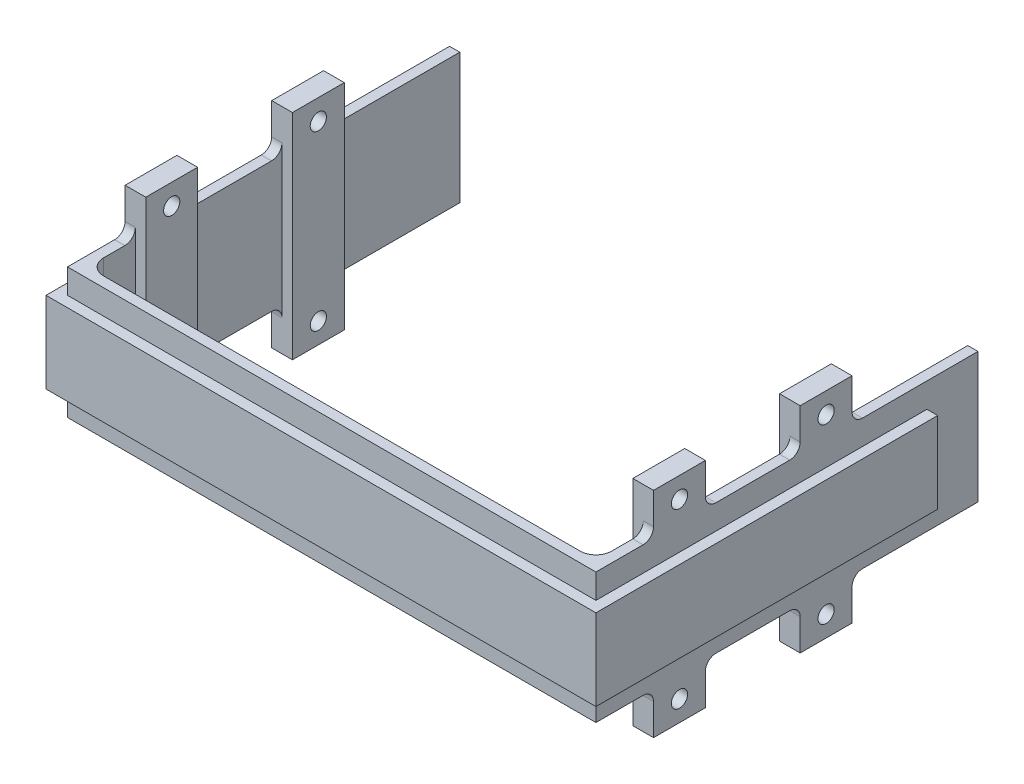
SolidWorks part; units mm, degrees
ref_plane "Front Plane" through (0, 0, 0) normal (0, 0, 1) x (1, 0, 0)
ref_plane "Top Plane" through (0, 0, 0) normal (0, 1, 0) x (1, 0, 0)
ref_plane "Right Plane" through (0, 0, 0) normal (1, 0, 0) x (0, 0, -1)
sketch "Sketch1" plane through (0, 0, 0) normal (0, 1, 0) x (1, 0, 0)
  line L1 (-52.5, 2) -> (52.5, 2)
  line L2 (-52.5, 2) -> (-52.5, -2)
  line L3 (-52.5, -2) -> (52.5, -2)
  line L4 (52.5, 2) -> (52.5, -2)
  line L5 (-52.5, 2) -> (52.5, -2) construction
  line L6 (-52.5, -2) -> (52.5, 2) construction
  line L7 (-52.5, 2) -> (-48.5, 2)
  line L8 (-52.5, 2) -> (-52.5, 63.25)
  line L9 (-52.5, 63.25) -> (-48.5, 63.25)
  line L10 (-48.5, 2) -> (-48.5, 63.25)
  line L11 (-48.5, 63.25) -> (-50.45, 63.25)
  line L12 (-48.5, 63.25) -> (-48.5, 73)
  line L13 (-48.5, 73) -> (-50.45, 73)
  line L14 (-50.45, 63.25) -> (-50.45, 73)
  line L15 (52.5, 2) -> (48.5, 2)
  line L16 (52.5, 2) -> (52.5, 63.25)
  line L17 (52.5, 63.25) -> (48.5, 63.25)
  line L18 (48.5, 2) -> (48.5, 63.25)
  line L19 (48.5, 63.25) -> (50.45, 63.25)
  line L20 (48.5, 63.25) -> (48.5, 73)
  line L21 (48.5, 73) -> (50.45, 73)
  line L22 (50.45, 63.25) -> (50.45, 73)
  point P0 (0, 0)
  dimension "D1" = 4
  dimension "D2" = 105
  dimension "D3" = 4
  dimension "D4" = 61.25
  dimension "D5" = 1.95
  dimension "D6" = 9.75
  dimension "D7" = 4
  dimension "D8" = 61.25
  dimension "D9" = 9.75
  dimension "D10" = 1.95
extrude "Boss-Extrude1" add sketch "Sketch1" along normal mid plane 24.9 contours L1 L10 L9 L8 | L14 L9 L12 L13 | L4 L1 L2 L3 | L18 L1 L16 L17 | L17 L22 L21 L20
sketch "Sketch2" plane through (48.5, 0, 0) normal (-1, 0, 0) x (0, 0, 1)
  line L0 (-2, -12.45) -> (-73, -12.45) construction
  line L1 (-11.05, -12.45) -> (-20.95, -12.45)
  line L2 (-11.05, -12.45) -> (-11.05, -20.45)
  line L3 (-11.05, -20.45) -> (-20.95, -20.45)
  line L4 (-20.95, -12.45) -> (-20.95, -20.45)
  line L5 (-2, 12.45) -> (-2, -12.45) construction
  line L6 (-4.4958, 0) -> (-73, 0) construction
  line L7 (-39.05, -12.45) -> (-48.95, -12.45)
  line L8 (-39.05, -12.45) -> (-39.05, -20.45)
  line L9 (-39.05, -20.45) -> (-48.95, -20.45)
  line L10 (-48.95, -12.45) -> (-48.95, -20.45)
  line L12 (-73, 12.45) -> (-73, -12.45) construction
  line L13 (-11.05, 20.45) -> (-20.95, 20.45)
  line L14 (-20.95, 12.45) -> (-20.95, 20.45)
  line L15 (-11.05, 12.45) -> (-20.95, 12.45)
  line L16 (-11.05, 12.45) -> (-11.05, 20.45)
  line L17 (-39.05, 20.45) -> (-48.95, 20.45)
  line L18 (-48.95, 12.45) -> (-48.95, 20.45)
  line L19 (-39.05, 12.45) -> (-48.95, 12.45)
  line L20 (-39.05, 12.45) -> (-39.05, 20.45)
  circle A0 centre (-16, -16.5) radius 1.55
  circle A1 centre (-44, -16.5) radius 1.55
  circle A2 centre (-16, 16.5) radius 1.55
  circle A3 centre (-44, 16.5) radius 1.55
  dimension "D4" = 3.1
  dimension "D5" = 3.95
  dimension "D8" = 4.95
  dimension "D10" = 3.1
  dimension "D11" = 3.95
  dimension "D12" = 4.95
  dimension "D1" = 9.05
  dimension "D2" = 9.9
  dimension "D3" = 8
  dimension "D6" = 8
  dimension "D7" = 9.9
  dimension "D9" = 18.1
extrude "Boss-Extrude2" add sketch "Sketch2" against normal blind 1.95 and the other way blind 2
sketch "Sketch3" plane through (46.5, 0, 0) normal (-1, 0, 0) x (0, 0, 1)
  line L1 (-48.95, -12.45) -> (-39.05, -12.45)
  line L2 (-48.95, -12.45) -> (-48.95, 12.45)
  line L3 (-48.95, 12.45) -> (-39.05, 12.45)
  line L4 (-39.05, -12.45) -> (-39.05, 12.45)
  line L5 (-20.95, -12.45) -> (-11.05, -12.45)
  line L6 (-20.95, -12.45) -> (-20.95, 12.45)
  line L7 (-20.95, 12.45) -> (-11.05, 12.45)
  line L8 (-11.05, -12.45) -> (-11.05, 12.45)
extrude "Boss-Extrude3" add sketch "Sketch3" against normal up to next
sketch "Sketch4" plane through (-48.5, 0, 0) normal (1, 0, 0) x (0, 0, -1)
  line L0 (2, 12.45) -> (73, 12.45) construction
  line L1 (11.05, 12.45) -> (20.95, 12.45)
  line L2 (11.05, 12.45) -> (11.05, 20.45)
  line L3 (11.05, 20.45) -> (20.95, 20.45)
  line L4 (20.95, 12.45) -> (20.95, 20.45)
  line L5 (2, 12.45) -> (2, -12.45) construction
  line L6 (2, 0) -> (73, 0) construction
  line L7 (39.05, 12.45) -> (48.95, 12.45)
  line L8 (39.05, 12.45) -> (39.05, 20.45)
  line L9 (39.05, 20.45) -> (48.95, 20.45)
  line L10 (48.95, 12.45) -> (48.95, 20.45)
  line L11 (73, 12.45) -> (73, -12.45) construction
  line L12 (39.05, -20.45) -> (48.95, -20.45)
  line L13 (48.95, -12.45) -> (48.95, -20.45)
  line L14 (39.05, -12.45) -> (48.95, -12.45)
  line L15 (39.05, -12.45) -> (39.05, -20.45)
  line L16 (11.05, -20.45) -> (20.95, -20.45)
  line L17 (20.95, -12.45) -> (20.95, -20.45)
  line L18 (11.05, -12.45) -> (20.95, -12.45)
  line L19 (11.05, -12.45) -> (11.05, -20.45)
  circle A0 centre (16, 16.5) radius 1.55
  circle A1 centre (44, 16.5) radius 1.55
  circle A2 centre (44, -16.5) radius 1.55
  circle A3 centre (16, -16.5) radius 1.55
  dimension "D4" = 3.1
  dimension "D5" = 3.95
  dimension "D6" = 4.95
  dimension "D10" = 3.1
  dimension "D11" = 4.95
  dimension "D12" = 3.95
  dimension "D1" = 9.05
  dimension "D2" = 9.9
  dimension "D3" = 8
  dimension "D7" = 9.9
  dimension "D8" = 8
  dimension "D9" = 18.1
extrude "Boss-Extrude4" add sketch "Sketch4" against normal blind 1.95 and the other way blind 2
sketch "Sketch5" plane through (-46.5, 0, 0) normal (1, 0, 0) x (0, 0, -1)
  line L1 (20.95, 12.45) -> (11.05, 12.45)
  line L2 (20.95, 12.45) -> (20.95, -12.45)
  line L3 (20.95, -12.45) -> (11.05, -12.45)
  line L4 (11.05, 12.45) -> (11.05, -12.45)
  line L5 (48.95, -12.45) -> (39.05, -12.45)
  line L6 (48.95, -12.45) -> (48.95, 12.45)
  line L7 (48.95, 12.45) -> (39.05, 12.45)
  line L8 (39.05, -12.45) -> (39.05, 12.45)
extrude "Boss-Extrude5" add sketch "Sketch5" against normal up to next
sketch "Sketch6" plane through (0, -12.45, 0) normal (0, -1, 0) x (1, 0, 0)
  line L1 (-50.45, -63.25) -> (-52.5, -63.25)
  line L2 (-50.45, -63.25) -> (-50.45, 2)
  line L3 (-50.45, 2) -> (-52.5, 2)
  line L4 (-52.5, -63.25) -> (-52.5, 2)
  line L5 (50.45, -63.25) -> (52.5, -63.25)
  line L6 (50.45, -63.25) -> (50.45, 2)
  line L7 (50.45, 2) -> (52.5, 2)
  line L8 (52.5, -63.25) -> (52.5, 2)
  line L9 (-50.45, 2) -> (50.45, 2)
  line L10 (-50.45, 2) -> (-50.45, -0.05)
  line L11 (-50.45, -0.05) -> (50.45, -0.05)
  line L12 (50.45, 2) -> (50.45, -0.05)
  line M17 (50.45, -63.25) -> (52.5, -63.25)
  line M18 (52.5, -63.25) -> (52.5, 2)
  line M19 (52.5, 2) -> (-52.5, 2)
  line M20 (-52.5, 2) -> (-52.5, -63.25)
  line M21 (-52.5, -63.25) -> (-50.45, -63.25)
  dimension "D1" = 2.05
extrude "Cut-Extrude1" cut sketch "Sketch6" against normal blind 4.7 contours L2 L11 L6 M19 | L6 M17 M18 M19 | L2 M21 M19 M20
sketch "Sketch7" plane through (0, 12.45, 0) normal (0, 1, 0) x (1, 0, 0)
  line L1 (-50.45, 63.25) -> (-52.5, 63.25)
  line L2 (-50.45, 63.25) -> (-50.45, -2)
  line L3 (-50.45, -2) -> (-52.5, -2)
  line L4 (-52.5, 63.25) -> (-52.5, -2)
  line L5 (50.45, 63.25) -> (52.5, 63.25)
  line L6 (50.45, 63.25) -> (50.45, -2)
  line L7 (50.45, -2) -> (52.5, -2)
  line L8 (52.5, 63.25) -> (52.5, -2)
  line L9 (-50.45, -2) -> (50.45, -2)
  line L10 (-50.45, -2) -> (-50.45, 0.05)
  line L11 (-50.45, 0.05) -> (50.45, 0.05)
  line L12 (50.45, -2) -> (50.45, 0.05)
  line M6 (-50.45, 39.05) -> (-50.45, 48.95)
  line M11 (-50.45, 63.25) -> (-52.5, 63.25)
  line M12 (-52.5, 63.25) -> (-52.5, -2)
  line M13 (-52.5, -2) -> (52.5, -2)
  line M14 (52.5, -2) -> (52.5, 63.25)
  line M15 (52.5, 63.25) -> (50.45, 63.25)
  line M20 (50.45, 48.95) -> (50.45, 39.05)
  line M24 (50.45, 20.95) -> (50.45, 11.05)
  line M30 (-50.45, 11.05) -> (-50.45, 20.95)
  dimension "D1" = 2.05
extrude "Cut-Extrude2" cut sketch "Sketch7" against normal blind 4.7 contours L2 M11 M12 M13 M30 M6 | L11 L2 L6 M13 | L6 M15 M20 M24 M13 M14
fillet "Fillet1" radius 2 16 edges at (-49.475, 12.45, -11.05) (-49.475, 12.45, -20.95) (-49.475, 12.45, -39.05) (-49.475, 12.45, -48.95) (-49.475, -12.45, -39.05) (-49.475, -12.45, -48.95) (-49.475, -12.45, -11.05) (-49.475, -12.45, -20.95) (49.475, -12.45, -20.95) (49.475, -12.45, -11.05) (49.475, -12.45, -48.95) (49.475, -12.45, -39.05) (49.475, 12.45, -11.05) (49.475, 12.45, -20.95) (49.475, 12.45, -48.95) (49.475, 12.45, -39.05)
fillet "Fillet2" radius 3 2 edges at (48.5, 0, -2) (-48.5, 0, -2)
